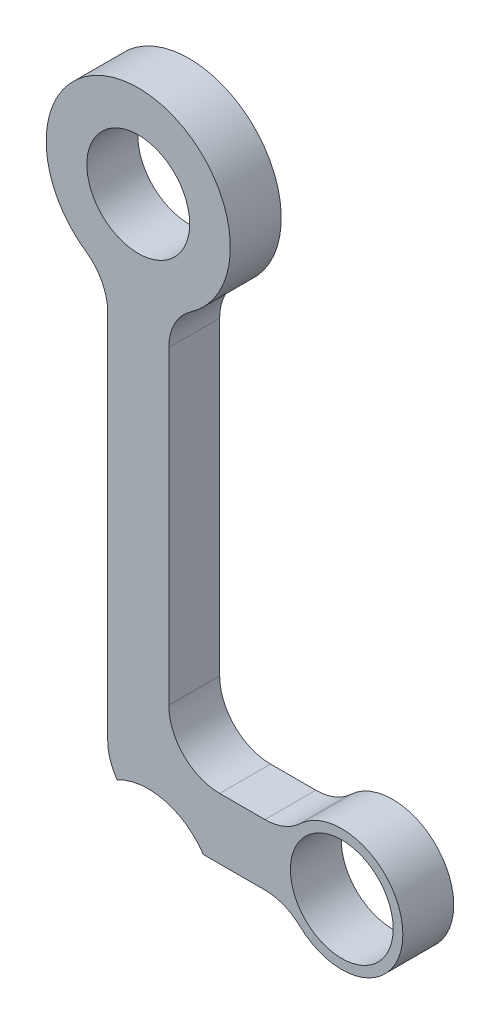
SolidWorks part; units mm, degrees
material "ABS"
ref_plane "Plan de face" through (0, 0, 0) normal (0, 0, 1) x (1, 0, 0)
ref_plane "Plan de dessus" through (0, 0, 0) normal (0, 1, 0) x (1, 0, 0)
ref_plane "Plan de droite" through (0, 0, 0) normal (1, 0, 0) x (0, 0, -1)
sketch "Esquisse1" plane through (0, 0, 0) normal (0, 0, 1) x (1, 0, 0)
  line L0 (0, 0) -> (0, -63.5) construction
  line L1 (-3.81, -14.6685) -> (-3.81, -60.96)
  line L2 (3.81, -14.6685) -> (3.81, -53.34)
  line L3 (0, -63.5) -> (25.4, -63.5) construction
  line L4 (2.54, -67.31) -> (15.8117, -67.31)
  line L5 (10.16, -59.69) -> (15.8117, -59.69)
  circle A0 centre (0, 0) radius 6.4135
  arc A1 (6.5443, -9.4484) -> (-6.5443, -9.4484) centre (0, 0) ccw
  circle A2 centre (0, -63.5) radius 3.81 construction
  arc A6 (-3.81, -14.6685) -> (-6.5443, -9.4484) centre (-10.16, -14.6685) ccw
  arc A7 (3.81, -14.6685) -> (6.5443, -9.4484) centre (10.16, -14.6685) cw
  circle A8 centre (25.4, -63.5) radius 6.4135
  arc A9 (20.17, -69.0418) -> (20.17, -57.9582) centre (25.4, -63.5) ccw
  arc A10 (10.16, -59.69) -> (3.81, -53.34) centre (10.16, -53.34) cw
  arc A11 (-3.81, -60.96) -> (2.54, -67.31) centre (2.54, -60.96) ccw
  arc A12 (15.8117, -59.69) -> (20.17, -57.9582) centre (15.8117, -53.34) ccw
  arc A13 (15.8117, -67.31) -> (20.17, -69.0418) centre (15.8117, -73.66) cw
  point P11 (3.81, -65.5585)
  point P17 (-3.81, -10.8436)
  point P20 (3.81, -10.8436)
  dimension "D2" = 12.827
  dimension "D3" = 5.08
  dimension "D5" = 63.5
  dimension "D6" = 25.4
  dimension "D4" = 12.827
  dimension "D1" = 7.62
  dimension "D7" = 6.35
  dimension "D8" = 6.35
  dimension "D9" = 7.62
extrude "Boss.-Extru.1" add sketch "Esquisse1" along normal blind 6.35
sketch "Esquisse5" plane through (0, 0, 0) normal (0, 0, -1) x (-1, 0, 0)
  circle A0 centre (-1.2541, -71.8976) radius 8.255
  dimension "D1" = 16.51
extrude "Enlèv. mat.-Extru.3" cut sketch "Esquisse5" against normal through all
